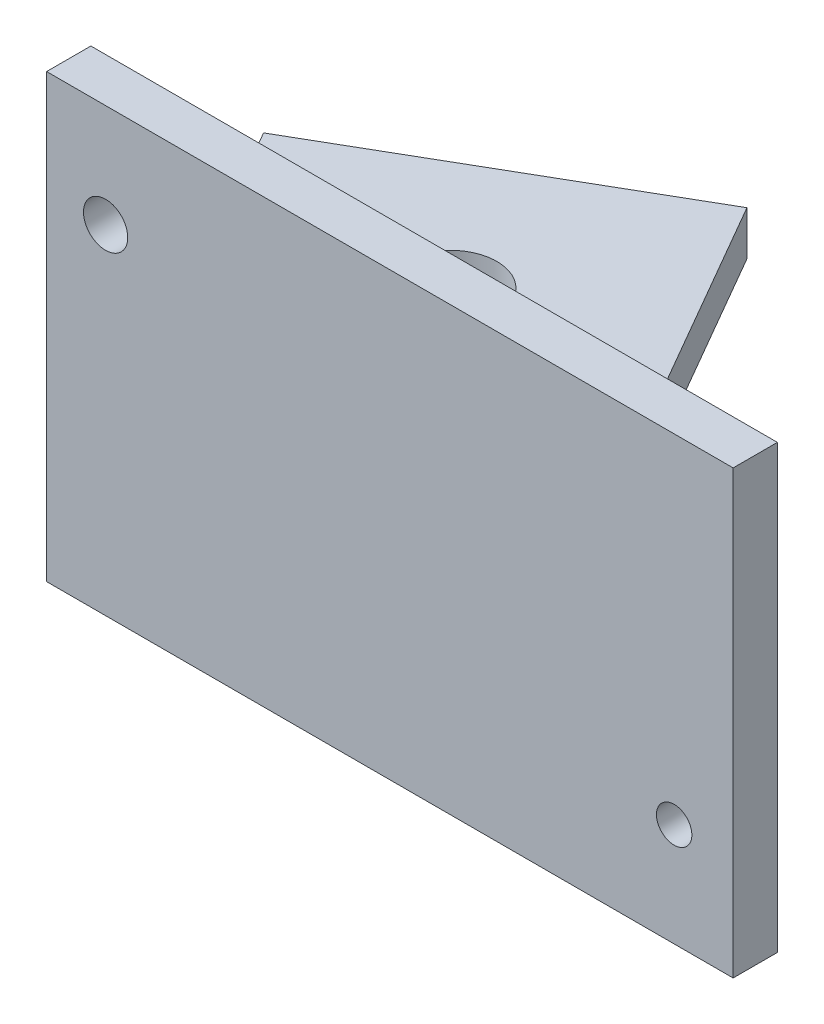
SolidWorks part; units mm, degrees
ref_plane "Front Plane" through (0, 0, 0) normal (0, 0, 1) x (1, 0, 0)
ref_plane "Top Plane" through (0, 0, 0) normal (0, 1, 0) x (1, 0, 0)
ref_plane "Right Plane" through (0, 0, 0) normal (1, 0, 0) x (0, 0, -1)
sketch "Sketch1" plane through (0, 0, 0) normal (0, 0, 1) x (1, 0, 0)
  line L1 (0, 0) -> (33.782, 0) construction
  line L2 (0, 0) -> (0, 19.812) construction
  line L3 (0, 19.812) -> (33.782, 19.812) construction
  line L4 (33.782, 0) -> (33.782, 19.812) construction
  line L5 (-1.5875, -1.5875) -> (35.3695, -1.5875)
  line L6 (-1.5875, -1.5875) -> (-1.5875, 19.812)
  line L7 (-1.5875, 19.812) -> (35.3695, 19.812)
  line L8 (35.3695, -1.5875) -> (35.3695, 19.812)
  circle A0 centre (1.5875, 14.2558) radius 1.1906
  circle A1 centre (32.1945, 1.5875) radius 0.9525
  dimension "D3" = 2.3813
  dimension "D4" = 1.905
  dimension "D5" = 1.5875
  dimension "D6" = 1.5875
  dimension "D7" = 1.5875
  dimension "D8" = 5.5562
  dimension "D9" = 3.175
  dimension "D11" = 3.175
  dimension "D12" = 5.5562
  dimension "D1" = 19.812
  dimension "D2" = 33.782
  dimension "D10" = 3.175
extrude "Boss-Extrude1" add sketch "Sketch1" along normal blind 2.3813
sketch "Sketch2" plane through (0, -1.5875, 0) normal (0, -1, 0) x (1, 0, 0)
  line L8 (-1.5875, 0) -> (20.4095, 0) construction
  line L9 (-1.5875, 2.3813) -> (35.3695, 2.3813)
  line L10 (-1.5875, 2.3813) -> (-1.5875, 0)
  line L12 (35.3695, 2.3813) -> (35.3695, 0)
  line L15 (2.2103, -31.522) -> (-14.2875, -21.997)
  line L16 (-1.5875, 0) -> (-14.2875, -21.997)
  line L17 (2.2103, -31.522) -> (20.4095, 0)
  line L18 (20.4095, 0) -> (35.3695, 0)
  dimension "D1" = 19.05
  dimension "D2" = 60
  dimension "D3" = 25.4
extrude "Boss-Extrude3" add sketch "Sketch2" along normal blind 2.3813
sketch "Sketch4" plane through (0, -1.5875, 0) normal (0, 1, 0) x (1, 0, 0)
  line L0 (-6.0386, 26.7595) -> (-2.019, 19.7973) construction
  line L1 (-14.2875, 21.997) -> (2.2103, 31.522) construction
  line L2 (-2.019, 19.7973) -> (4.331, 8.7988) construction
  line L3 (4.331, 8.7988) -> (9.411, 0) construction
  line L4 (-1.5875, 0) -> (20.4095, 0) construction
  circle A0 centre (-2.019, 19.7973) radius 2.4892
  circle A1 centre (4.331, 8.7988) radius 2.4892
  dimension "D1" = 4.9784
  dimension "D2" = 12.7
  dimension "D3" = 10.16
extrude "Cut-Extrude2" cut sketch "Sketch4" against normal up to next
fillet "Fillet1" radius 2.54 1 edges at (9.411, -1.5875, 0)
